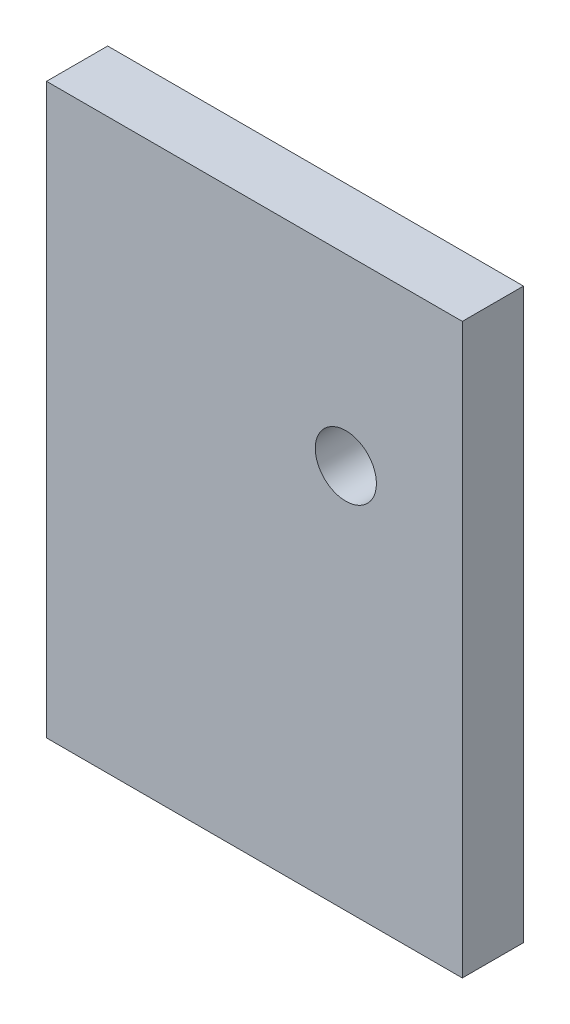
SolidWorks part; units mm, degrees
ref_plane "Alzado" through (0, 0, 0) normal (0, 0, 1) x (1, 0, 0)
ref_plane "Planta" through (0, 0, 0) normal (0, 1, 0) x (1, 0, 0)
ref_plane "Vista lateral" through (0, 0, 0) normal (1, 0, 0) x (0, 0, -1)
sketch "Croquis1" plane through (0, 0, 0) normal (0, 0, 1) x (1, 0, 0)
  line L1 (-54.8277, 48.1512) -> (13.1723, 48.1512)
  line L2 (-54.8277, 48.1512) -> (-54.8277, -44.8488)
  line L3 (-54.8277, -44.8488) -> (13.1723, -44.8488)
  line L4 (13.1723, 48.1512) -> (13.1723, -44.8488)
  dimension "D1" = 93
  dimension "D2" = 68
extrude "Saliente-Extruir1" add sketch "Croquis1" along normal blind 10
sketch "Croquis2" plane through (0, 0, 10) normal (0, 0, 1) x (1, 0, 0)
  line L0 (-54.8277, 48.1512) -> (-54.8277, -44.8488) construction
  line L1 (-54.8277, -44.8488) -> (13.1723, -44.8488) construction
  circle A0 centre (-5.8777, 18.1512) radius 5
  dimension "D1" = 10
  dimension "D2" = 48.95
  dimension "D3" = 63
extrude "Cortar-Extruir1" cut sketch "Croquis2" against normal through all
